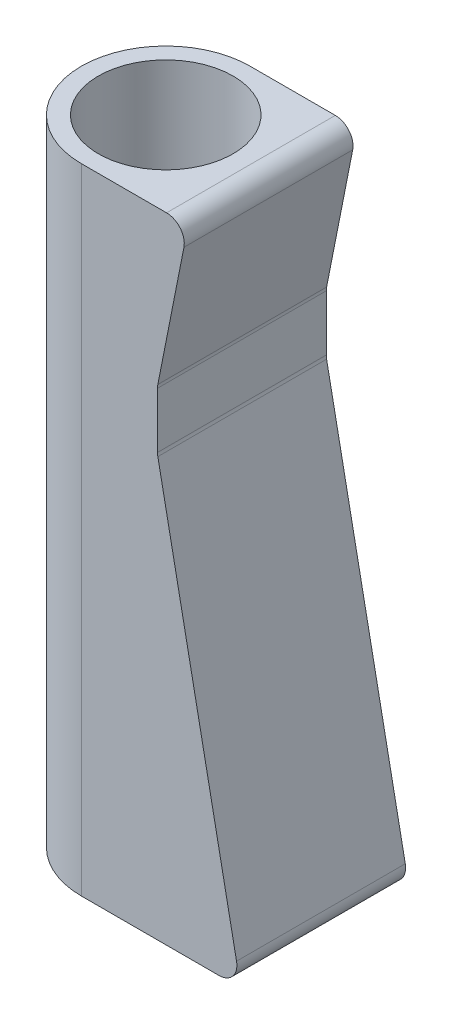
SolidWorks part; units mm, degrees
ref_plane "Front Plane" through (0, 0, 0) normal (0, 0, 1) x (1, 0, 0)
ref_plane "Top Plane" through (0, 0, 0) normal (0, 1, 0) x (1, 0, 0)
ref_plane "Right Plane" through (0, 0, 0) normal (1, 0, 0) x (0, 0, -1)
sketch "Sketch1" plane through (0, 0, 0) normal (0, 1, 0) x (1, 0, 0)
  circle A0 centre (0, 0) radius 11.4125
  circle A1 centre (0, 0) radius 14.2875
  dimension "D1" = 22.825
  dimension "D2" = 28.575
extrude "Boss-Extrude1" add sketch "Sketch1" along normal blind 152.4
ref_plane "Plane1" through (14.2875, 0, 0) normal (1, 0, 0) x (0, 0, -1)
sketch "Sketch2" plane through (14.2875, 0, 0) normal (1, 0, 0) x (0, 0, -1)
  line L1 (14.2875, 0) -> (-14.2875, 0)
  line L2 (14.2875, 0) -> (14.2875, 152.4)
  line L3 (14.2875, 152.4) -> (-14.2875, 152.4)
  line L4 (-14.2875, 0) -> (-14.2875, 152.4)
extrude "Boss-Extrude2" add sketch "Sketch2" along normal blind 12.7 separate body
sketch "Sketch3" plane through (0, 152.4, 0) normal (0, 1, 0) x (1, 0, 0)
  line L0 (14.2875, -14.2875) -> (0, -14.2875)
  line L1 (14.2875, 14.2875) -> (0, 14.2875)
  line L4 (14.2875, 14.2875) -> (14.2875, -14.2875)
  line L5 (14.2875, -14.2875) -> (26.9875, -14.2875)
  line L6 (26.9875, -14.2875) -> (26.9875, 14.2875)
  line L7 (26.9875, 14.2875) -> (14.2875, 14.2875)
  line L9 (14.2875, -14.2875) -> (26.9875, -14.2875)
  line L10 (26.9875, -14.2875) -> (26.9875, 14.2875)
  line L11 (26.9875, 14.2875) -> (14.2875, 14.2875)
  arc A0 (0, -14.2875) -> (0, 14.2875) centre (0, 0) ccw
  dimension "D1" = 0
extrude "Boss-Extrude3" add sketch "Sketch3" against normal through all
sketch "Sketch5" plane through (0, 0, 14.2875) normal (0, 0, 1) x (1, 0, 0)
  line L3 (26.9875, 0) -> (12.8972, 71.2)
  line L5 (26.9875, 0) -> (26.9875, 152.4)
  line L6 (12.8972, 71.2) -> (12.8972, 81.2)
  line L7 (12.8972, 81.2) -> (26.9875, 152.4)
  dimension "D1" = 10
  dimension "D2" = 71.2
  dimension "D3" = 71.2
extrude "Cut-Extrude1" cut sketch "Sketch5" against normal through all
fillet "Fillet1" radius 3 4 edges at (26.9875, 152.4, 0) (12.8972, 81.2, 0) (12.8972, 71.2, 0) (26.9875, 0, 0)
sketch "Sketch6" plane through (0, 0, 14.2875) normal (0, 0, 1) x (1, 0, 0)
  line L0 (0, 152.4) -> (23.3356, 152.4) construction
  line L1 (34.7125, 107.4) -> (-15.2875, 107.4)
  line L2 (34.7125, 107.4) -> (34.7125, 152.4)
  line L3 (34.7125, 152.4) -> (-15.2875, 152.4)
  line L4 (-15.2875, 107.4) -> (-15.2875, 152.4)
  line L5 (-14.2875, 152.4) -> (-14.2875, 0) construction
  dimension "D1" = 0
  dimension "D2" = 1
  dimension "D3" = 50
  dimension "D4" = 45
extrude "Cut-Extrude2" cut sketch "Sketch6" against normal blind 82
fillet "Fillet2" radius 3 1 edges at (18.0821, 107.4, 0)
